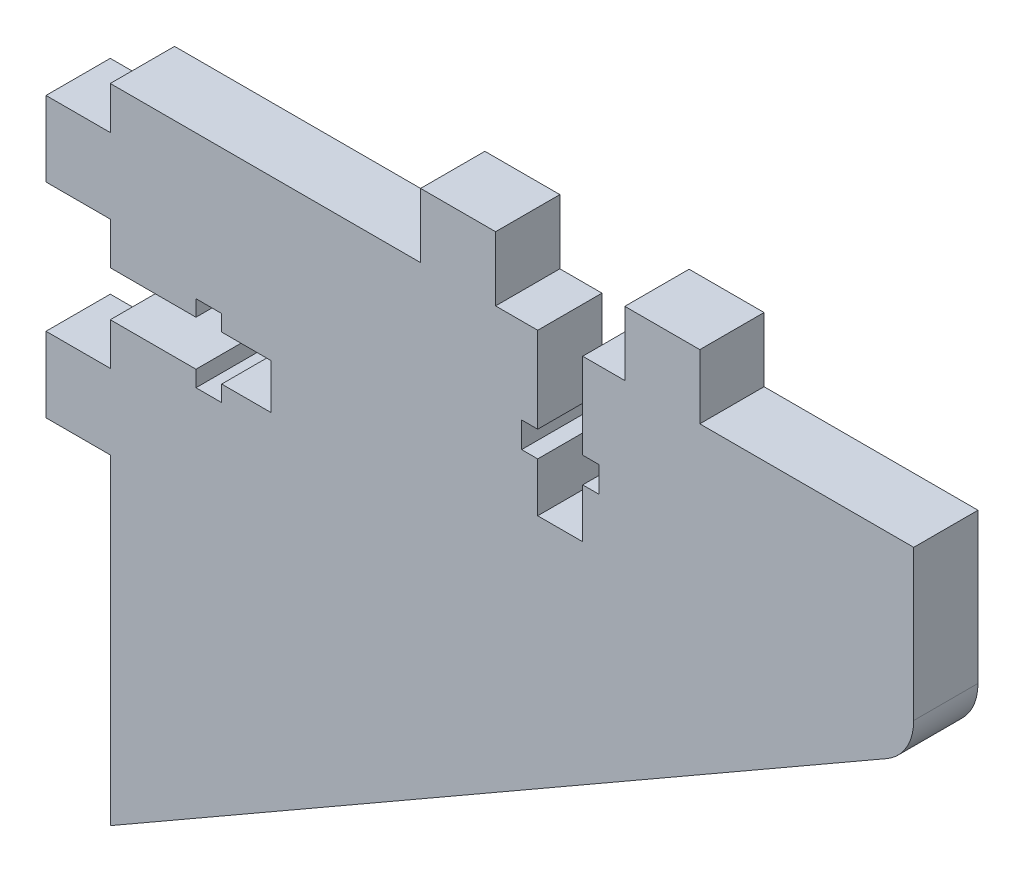
SolidWorks part; units mm, degrees
material "Клен"
ref_plane "Спереди" through (0, 0, 0) normal (0, 0, 1) x (1, 0, 0)
ref_plane "Сверху" through (0, 0, 0) normal (0, 1, 0) x (1, 0, 0)
ref_plane "Справа" through (0, 0, 0) normal (1, 0, 0) x (0, 0, -1)
sketch "Эскиз1" plane through (0, 0, 0) normal (0, 0, 1) x (1, 0, 0)
  line L0 (81, -293.8462) -> (81, -307.8462)
  line L4 (78.4916, -312.1811) -> (6, -353.8462)
  line L5 (6, -293.8462) -> (6, -353.8462)
  line L6 (81, -287.8462) -> (81, -293.8462) construction
  line L9 (81, -293.8462) -> (6, -293.8462)
  arc A0 (81, -307.8462) -> (78.4916, -312.1811) centre (76, -307.8462) cw
  dimension "D3" = 5
  dimension "D1" = 60
  dimension "D2" = 75
  dimension "D4" = 14
extrude "Бобышка-Вытянуть1" add sketch "Эскиз1" against normal blind 6 contours L9 L5 L4 A0 L0
sketch "Эскиз2" plane through (56, -310.8462, 0) normal (0, 0, 1) x (0, 1, 0)
  line L1 (-13.0318, 50) -> (-6.0318, 50)
  line L2 (-13.0318, 50) -> (-13.0318, 56)
  line L3 (-13.0318, 56) -> (-6.0318, 56)
  line L4 (-6.0318, 50) -> (-6.0318, 56)
  line L5 (13, 56) -> (-13, 56) construction
  line L7 (13.0318, 50) -> (6.0318, 50)
  line L8 (6.0318, 50) -> (6.0318, 56)
  line L9 (13.0318, 56) -> (6.0318, 56)
  line L10 (13.0318, 50) -> (13.0318, 56)
  dimension "D1" = 7
extrude "Бобышка-Вытянуть2" add sketch "Эскиз2" against normal blind 6
sketch "Эскиз3" plane through (56, -310.8462, 0) normal (0, 0, 1) x (0, 1, 0)
  line L3 (-2.1, 42) -> (-3.6, 42)
  line L4 (-3.6, 42) -> (-3.6, 39.6)
  line L5 (-3.6, 39.6) -> (-2.1, 39.6)
  line L11 (3.6, 39.6) -> (2.1, 39.6)
  line L12 (3.6, 42) -> (3.6, 39.6)
  line L13 (2.1, 42) -> (3.6, 42)
  line L16 (-2.1, 42) -> (-2.1, 50)
  line L17 (-2.1, 50) -> (2.1, 50)
  line L18 (2.1, 50) -> (2.1, 42)
  line L19 (2.1, 39.6) -> (2.1, 35)
  line L20 (2.1, 35) -> (-2.1, 35)
  line L21 (-2.1, 35) -> (-2.1, 39.6)
  line L22 (13, 50) -> (-13, 50) construction
  point P15 (0, 43.65)
  point P20 (0, 50)
  dimension "D2" = 7.2
  dimension "D3" = 2.4
  dimension "D4" = 4.2
  dimension "D5" = 15
extrude "Вырез-Вытянуть1" cut sketch "Эскиз3" against normal through all
other "Авто-элемент1<DIN967-20>"
sketch "Эскиз21" plane through (48, -343.8462, 0) normal (0, 0, 1) x (1, 0, 0)
  line L1 (-13.0318, 50) -> (-6.0318, 50)
  line L2 (-13.0318, 50) -> (-13.0318, 56)
  line L3 (-13.0318, 56) -> (-6.0318, 56)
  line L4 (-6.0318, 50) -> (-6.0318, 56)
  line L5 (13, 56) -> (-13, 56) construction
  line L7 (13.0318, 50) -> (6.0318, 50)
  line L8 (6.0318, 50) -> (6.0318, 56)
  line L9 (13.0318, 56) -> (6.0318, 56)
  line L10 (13.0318, 50) -> (13.0318, 56)
  dimension "D1" = 7
extrude "Бобышка-Вытянуть21" add sketch "Эскиз21" against normal blind 6
sketch "Эскиз31" plane through (48, -343.8462, 0) normal (0, 0, 1) x (1, 0, 0)
  line L3 (-2.1, 42) -> (-3.6, 42)
  line L4 (-3.6, 42) -> (-3.6, 39.6)
  line L5 (-3.6, 39.6) -> (-2.1, 39.6)
  line L11 (3.6, 39.6) -> (2.1, 39.6)
  line L12 (3.6, 42) -> (3.6, 39.6)
  line L13 (2.1, 42) -> (3.6, 42)
  line L16 (-2.1, 42) -> (-2.1, 50)
  line L17 (-2.1, 50) -> (2.1, 50)
  line L18 (2.1, 50) -> (2.1, 42)
  line L19 (2.1, 39.6) -> (2.1, 35)
  line L20 (2.1, 35) -> (-2.1, 35)
  line L21 (-2.1, 35) -> (-2.1, 39.6)
  line L22 (13, 50) -> (-13, 50) construction
  point P15 (0, 43.65)
  point P20 (0, 50)
  dimension "D2" = 7.2
  dimension "D3" = 2.4
  dimension "D4" = 4.2
  dimension "D5" = 15
extrude "Вырез-Вытянуть11" cut sketch "Эскиз31" against normal through all
other "Авто-элемент2<DIN967-21>"
